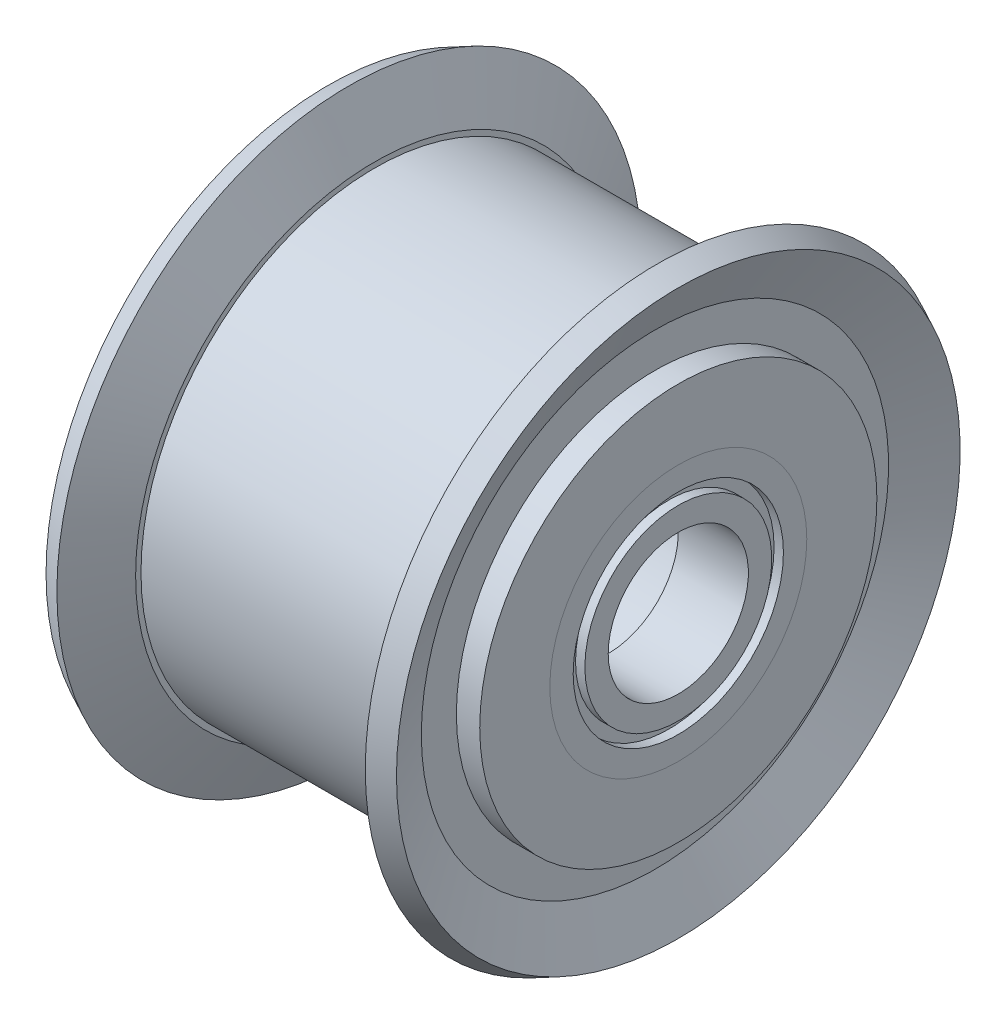
SolidWorks part; units mm, degrees
material "1060 Alloy"
ref_plane "Front Plane" through (0, 0, 0) normal (0, 0, 1) x (1, 0, 0)
ref_plane "Top Plane" through (0, 0, 0) normal (0, 1, 0) x (1, 0, 0)
ref_plane "Right Plane" through (0, 0, 0) normal (1, 0, 0) x (0, 0, -1)
sketch "Sketch1" plane through (0, 0, 0) normal (0, 0, 1) x (1, 0, 0)
  line L0 (-5.5, 10) -> (5.5, 10)
  line L1 (5.5, 10) -> (5.5, 8.5)
  line L2 (5.5, 8.5) -> (7.5, 8.5)
  line L3 (7.5, 8.5) -> (7.5, 5.5)
  line L4 (7.5, 5.5) -> (4.5, 5.5)
  line L5 (4.5, 5.5) -> (4.5, 5)
  line L6 (4.5, 5) -> (-4.5, 5)
  line L7 (-4.5, 5) -> (-4.5, 5.5)
  line L8 (-4.5, 5.5) -> (-7.5, 5.5)
  line L9 (-7.5, 5.5) -> (-7.5, 8.5)
  line L10 (-7.5, 8.5) -> (-5.5, 8.5)
  line L11 (-5.5, 8.5) -> (-5.5, 10)
  line L12 (0, 0) -> (0, 13.5671) construction
  line L13 (0, 0) -> (19.4675, 0) construction
  dimension "D1" = 10
  dimension "D2" = 11
  dimension "D3" = 20
  dimension "D4" = 17
  dimension "D5" = 11
  dimension "D6" = 15
  dimension "D7" = 3
revolve "Revolve1" add sketch "Sketch1" angle 360 about L13
sketch "Sketch2" plane through (0, 0, 0) normal (0, 0, 1) x (1, 0, 0)
  line L0 (5.5, 10.2295) -> (5.5, 8.5)
  line L1 (5.5, 8.5) -> (6.5, 8.5)
  line L2 (6.5, 8.5) -> (6.5, 10)
  line L3 (6.5, 10) -> (7.5, 12.064)
  line L4 (7.5, 12.064) -> (6.6001, 12.5)
  line L5 (6.6001, 12.5) -> (5.5, 10.2295)
  line L6 (7.5, 8.5) -> (5.5, 8.5) construction
  line L7 (5.5, -10) -> (5.5, 10) construction
  line L8 (0, 0) -> (8.7636, 0) construction
  line L9 (0, 0) -> (0, 14.1418) construction
  line L10 (-6.5, 8.5) -> (-6.5, 10)
  line L11 (-5.5, 8.5) -> (-6.5, 8.5)
  line L12 (-5.5, 10.2295) -> (-5.5, 8.5)
  line L13 (-6.5, 10) -> (-7.5, 12.064)
  line L14 (-7.5, 12.064) -> (-6.6001, 12.5)
  line L15 (-6.6001, 12.5) -> (-5.5, 10.2295)
  line L16 (5.5, 10) -> (-5.5, 10) construction
  line L17 (7.5, -8.5) -> (7.5, 8.5) construction
  dimension "D1" = 25
  dimension "D2" = 1
revolve "Revolve2" add sketch "Sketch2" angle 360 about L8
sketch "Sketch3" plane through (0, 0, 0) normal (0, 0, 1) x (1, 0, 0)
  line L0 (0, 0) -> (21.9602, 0) construction
  line L1 (4.5, 5.5) -> (7.5, 5.5)
  line L2 (4.5, 5.5) -> (4.5, 4.5)
  line L3 (4.5, 3) -> (7.5, 3)
  line L4 (7.5, 5.5) -> (7.5, 4.5)
  line L5 (0, 0) -> (0, 16.4398) construction
  line L6 (4.5, 4.5) -> (4.9, 4.5)
  line L7 (4.9, 4.5) -> (4.9, 4)
  line L8 (4.9, 4) -> (4.5, 4)
  line L9 (7.5, 4.5) -> (7.1, 4.5)
  line L10 (7.1, 4.5) -> (7.1, 4)
  line L11 (7.1, 4) -> (7.5, 4)
  line L12 (4.5, 4) -> (4.5, 3)
  line L13 (7.5, 4) -> (7.5, 3)
  line L14 (7.5, 5.5) -> (4.5, 5.5) construction
  line L15 (4.5, -5.5) -> (4.5, 5.5) construction
  line L16 (-4.5, 4.5) -> (-4.9, 4.5)
  line L17 (-4.9, 4.5) -> (-4.9, 4)
  line L18 (-4.9, 4) -> (-4.5, 4)
  line L19 (-4.5, 4) -> (-4.5, 3)
  line L20 (-4.5, 3) -> (-7.5, 3)
  line L21 (-7.5, 4) -> (-7.5, 3)
  line L22 (-7.1, 4) -> (-7.5, 4)
  line L23 (-7.1, 4.5) -> (-7.1, 4)
  line L24 (-7.5, 4.5) -> (-7.1, 4.5)
  line L25 (-7.5, 5.5) -> (-7.5, 4.5)
  line L26 (-4.5, 5.5) -> (-4.5, 4.5)
  line L27 (-4.5, 5.5) -> (-7.5, 5.5)
  dimension "D1" = 6
  dimension "D2" = 3
  dimension "D3" = 0.5
  dimension "D4" = 0.4
revolve "Revolve3" add sketch "Sketch3" angle 360 about L0
